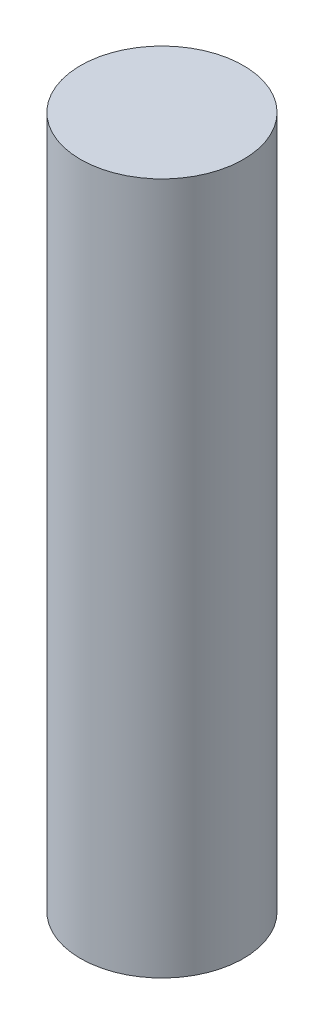
SolidWorks part; units mm, degrees
ref_plane "Спереди" through (0, 0, 0) normal (0, 0, 1) x (1, 0, 0)
ref_plane "Сверху" through (0, 0, 0) normal (0, 1, 0) x (1, 0, 0)
ref_plane "Справа" through (0, 0, 0) normal (1, 0, 0) x (0, 0, -1)
other "Центр тяжести"
sketch "Эскиз1" plane through (0, 0, 0) normal (0, 1, 0) x (1, 0, 0)
  circle A0 centre (0, 0) radius 10
  dimension "D1" = 20
extrude "Бобышка-Вытянуть1" add sketch "Эскиз1" along normal blind 85
sketch "Эскиз2" plane through (0, 0, 0) normal (0, -1, 0) x (1, 0, 0)
  circle A0 centre (0, 0) radius 2
  dimension "D1" = 4
extrude "Вырез-Вытянуть1" cut sketch "Эскиз2" against normal blind 60
